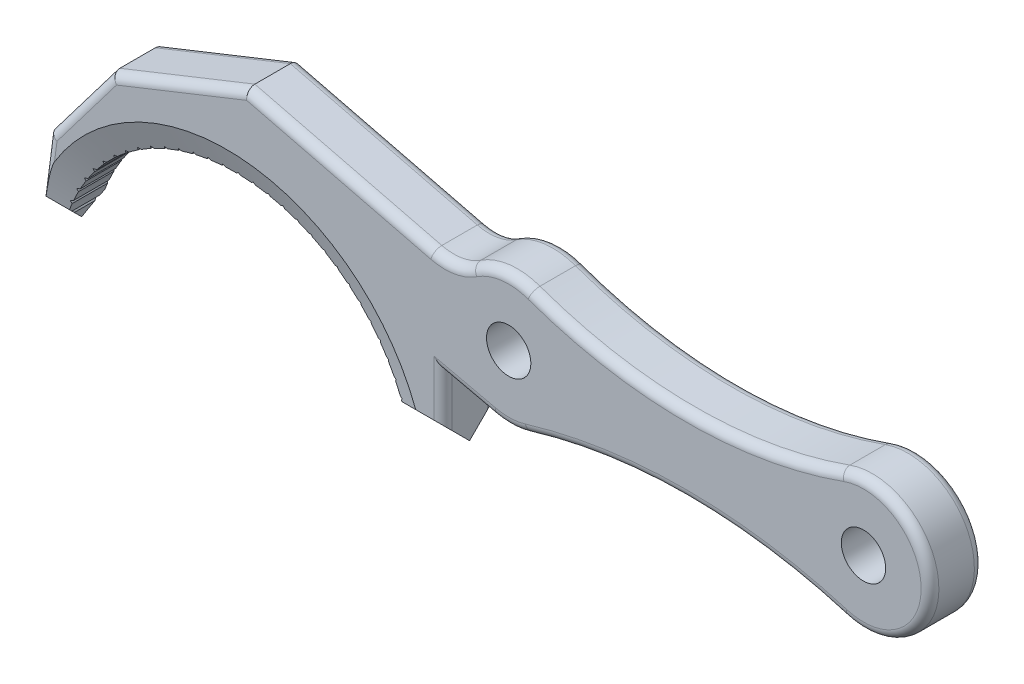
SolidWorks part; units mm, degrees
ref_plane "Front Plane" through (0, 0, 0) normal (0, 0, 1) x (1, 0, 0)
ref_plane "Top Plane" through (0, 0, 0) normal (0, 1, 0) x (1, 0, 0)
ref_plane "Right Plane" through (0, 0, 0) normal (1, 0, 0) x (0, 0, -1)
sketch "Sketch1" plane through (0, 0, 0) normal (0, 0, 1) x (1, 0, 0)
  line L0 (0, 0) -> (50000, 0) construction
  line L1 (24.5934, 0) -> (30.9434, 0)
  line L2 (30.9434, 0) -> (30.9434, 10.16)
  line L3 (30.9434, 10.16) -> (38.2289, 8.4945)
  line L4 (-24.5934, 0) -> (-27.0775, 0)
  line L5 (-27.0775, 0) -> (-25.5277, 11.9038)
  line L6 (-25.5277, 11.9038) -> (-16.5858, 23.6869)
  line L7 (-16.5858, 23.6869) -> (2.7457, 31.3837)
  line L8 (2.7457, 31.3837) -> (29.5138, 24.765)
  line L10 (0, 0) -> (-25.5277, 11.9038) construction
  line L11 (0, 0) -> (-16.5858, 23.6869) construction
  line L12 (0, 0) -> (2.7457, 31.3837) construction
  line L13 (0, 0) -> (29.5138, 24.765) construction
  circle A0 centre (0, -6.35) radius 25.4 construction
  arc A1 (24.5934, 0) -> (-24.5934, 0) centre (0, -6.35) ccw
  circle A3 centre (40.3515, 17.78) radius 9.525 construction
  circle A4 centre (40.3515, 17.78) radius 3.175
  circle A5 centre (91.1515, 17.78) radius 9.525 construction
  circle A6 centre (91.1515, 17.78) radius 3.175
  arc A7 (87.9321, 26.7444) -> (88.4068, 8.659) centre (91.1515, 17.78) cw
  arc A10 (87.9321, 26.7444) -> (43.571, 26.7444) centre (65.7515, 88.5052) cw
  arc A11 (88.4068, 8.659) -> (43.0963, 8.659) centre (65.7515, -66.6265) ccw
  arc A12 (29.5138, 24.765) -> (35.1023, 25.728) centre (31.2093, 31.6224) ccw
  arc A13 (35.1023, 25.728) -> (43.571, 26.7444) centre (40.3515, 17.78) cw
  arc A14 (43.0963, 8.659) -> (38.2289, 8.4945) centre (40.3515, 17.78) cw
  dimension "D2" = 50.8
  dimension "D7" = 19.05
  dimension "D9" = 6.35
  dimension "D10" = 6.35
  dimension "D1" = 6.35
  dimension "D3" = 25
  dimension "D4" = 30
  dimension "D5" = 40
  dimension "D6" = 45
  dimension "D8" = 17.78
  dimension "D11" = 10.16
  dimension "D12" = 50.8
extrude "Boss-Extrude1" add sketch "Sketch1" along normal mid plane 7.62
sketch "Sketch2" plane through (0, 0, 0) normal (1, 0, 0) x (0, 0, -1)
  line L0 (0, 0) -> (3.81, 3.81)
  line L1 (3.81, 0) -> (3.81, 10.16) construction
  line L2 (3.81, 3.81) -> (3.81, 0)
  line L3 (3.81, 0) -> (0, 0)
  dimension "D1" = 45
extrude "Cut-Extrude1" cut sketch "Sketch2" against normal through all both and the other way through all
mirror "Mirror1" about plane through (0, 0, 0) normal (0, 0, 1) of "Cut-Extrude1"
chamfer "Chamfer1" distance 1.27 angle 70 2 edges at (0, 19.05, -3.81) (0, 19.05, 3.81)
sketch "Sketch4" plane through (0, 0, 3.81) normal (0, 0, 1) x (1, 0, 0)
  line L3 (23.939, 3.0395) -> (22.0842, -0.4453)
  line L4 (22.0842, -0.4453) -> (20.2096, 4.3341)
  line L5 (20.2096, 4.3341) -> (23.939, 3.0395)
  circle A0 centre (0, -6.35) radius 22.86 construction
  arc A1 (23.7934, 2.54) -> (-23.7934, 2.54) centre (0, -6.35) ccw construction
  dimension "D1" = 2.54
extrude "Cut-Extrude2" cut sketch "Sketch4" against normal through all
pattern_circular "CirPattern1" count 30 over 140 about axis through (0, -6.35, 0) along (0, 0, 1) of "Cut-Extrude2"
fillet "Fillet1" radius 1.27 24 edges at (34.5861, 9.3273, -3.81) (40.6732, 8.2604, -3.81) (65.7515, 11.9939, -3.81) (100.6733, 18.0299, -3.81) (16.1297, 28.0743, -3.81) (32.4089, 24.6611, -3.81) (39.2165, 27.2371, -3.81) (34.5861, 9.3273, 3.81) (40.6732, 8.2604, 3.81) (65.7515, 11.9939, 3.81) (100.6733, 18.0299, 3.81) (16.1297, 28.0743, 3.81) (32.4089, 24.6611, 3.81) (39.2165, 27.2371, 3.81) (30.9434, 6.985, -3.81) (30.9434, 6.985, 3.81) (65.7515, 22.8823, -3.81) (65.7515, 22.8823, 3.81) (-25.9475, 8.6794, -3.81) (-25.9475, 8.6794, 3.81) (-21.0568, 17.7954, 3.81) (-21.0568, 17.7954, -3.81) (-6.92, 27.5353, -3.81) (-6.92, 27.5353, 3.81)
